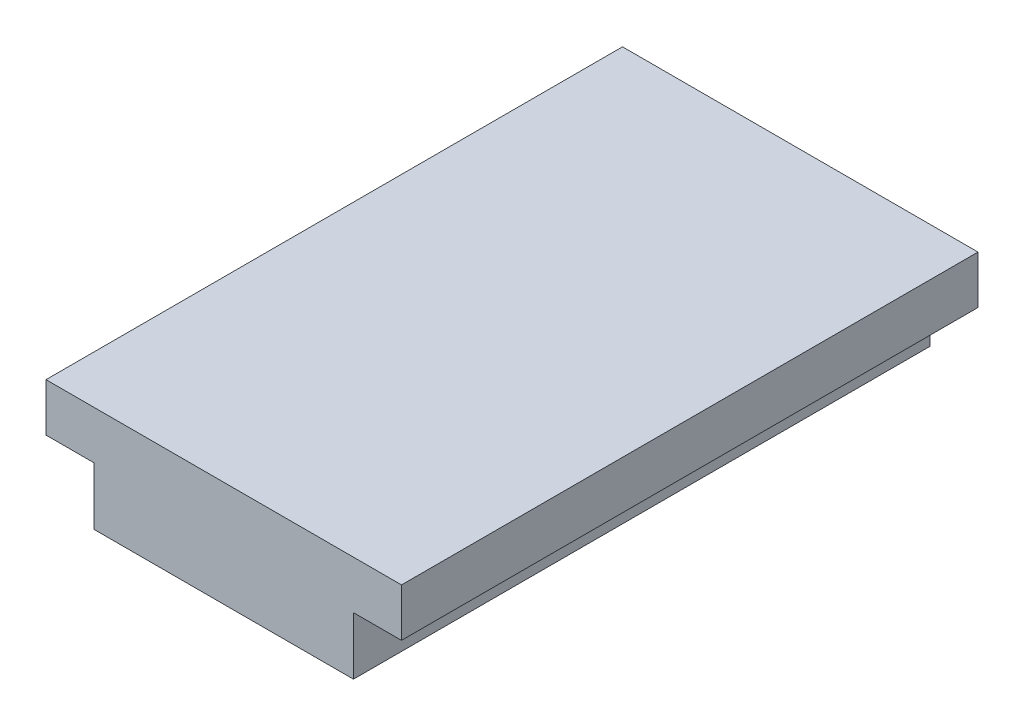
SolidWorks part; units mm, degrees
ref_plane "Front Plane" through (0, 0, 0) normal (0, 0, 1) x (1, 0, 0)
ref_plane "Top Plane" through (0, 0, 0) normal (0, 1, 0) x (1, 0, 0)
ref_plane "Right Plane" through (0, 0, 0) normal (1, 0, 0) x (0, 0, -1)
sketch "Sketch1" plane through (0, 0, 0) normal (0, 0, 1) x (1, 0, 0)
  line L0 (-14.5327, 0) -> (15.0108, 0) construction
  line L1 (-14.5327, 3) -> (15.0108, 3) construction
  line L2 (-7.0544, 7.4288) -> (-7.0544, -5.7452) construction
  line L3 (6.4456, 7.4288) -> (6.4456, -6.2886) construction
  line L4 (-12.5109, 5.5) -> (12.9021, 5.5) construction
  line L5 (-9.5544, 7.4288) -> (-9.5544, -5.3756) construction
  line L6 (8.9456, 7.4288) -> (8.9456, -6.5278) construction
  line L7 (-7.0544, 0) -> (-7.0544, 3)
  line L8 (-7.0544, 3) -> (-9.5544, 3)
  line L9 (-9.5544, 3) -> (-9.5544, 5.5)
  line L10 (-9.5544, 5.5) -> (8.9456, 5.5)
  line L11 (8.9456, 5.5) -> (8.9456, 3)
  line L12 (8.9456, 3) -> (6.4456, 3)
  line L13 (6.4456, 3) -> (6.4456, 0)
  line L14 (6.4456, 0) -> (-7.0544, 0)
  dimension "D1" = 13.5
  dimension "D2" = 18.5
  dimension "D3" = 2.5
  dimension "D4" = 2.5
  dimension "D5" = 3
  dimension "D6" = 2.5
extrude "Boss-Extrude1" add sketch "Sketch1" along normal blind 30
sketch "Sketch2" plane through (0, 0, 0) normal (0, 0, -1) x (-1, 0, 0)
  text T0 "2.5\r\n" font "Century Gothic" height in points 7
  text T1 "13.5" font "Century Gothic" height in points 7
  text T2 "18.5" font "Century Gothic" height in points 7
extrude "Cut-Extrude1" cut sketch "Sketch2" against normal blind 1
sketch "Sketch3" plane through (-9.5544, 0, 0) normal (-1, 0, 0) x (0, 0, 1)
  text T0 "2.5" font "Century Gothic" height in points 7
extrude "Cut-Extrude3" cut sketch "Sketch3" against normal blind 1
